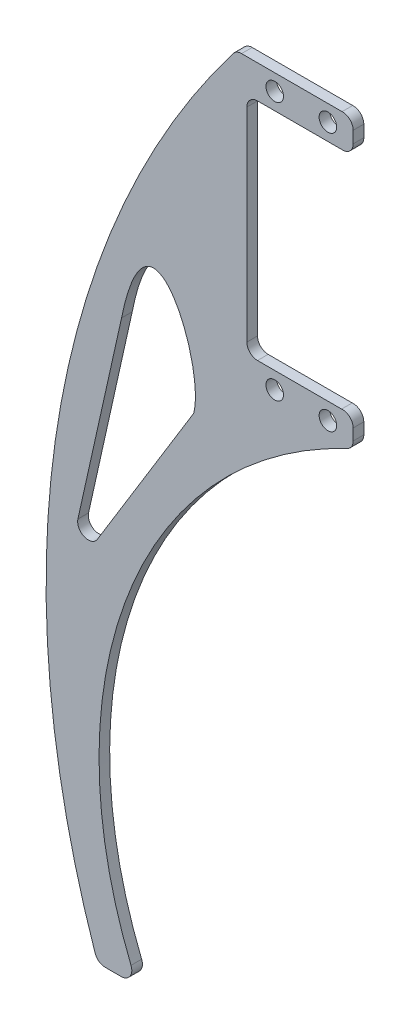
SolidWorks part; units mm, degrees
ref_plane "前视基准面" through (0, 0, 0) normal (0, 0, 1) x (1, 0, 0)
ref_plane "上视基准面" through (0, 0, 0) normal (0, 1, 0) x (1, 0, 0)
ref_plane "右视基准面" through (0, 0, 0) normal (1, 0, 0) x (0, 0, -1)
sketch "草图1" plane through (0, 0, 0) normal (0, 0, 1) x (1, 0, 0)
  line L0 (1.4233, 0) -> (4.4233, 0)
  line L1 (27.0735, 161.7067) -> (45.9834, 161.7067)
  line L3 (48.0729, 111.2078) -> (48.0729, 109.0876)
  line L4 (46.203, 155.5) -> (30.0729, 155.5)
  line L5 (-3.7143, 70.4778) -> (4.4985, 107.3478)
  line L7 (28.0729, 153.5) -> (28.0729, 115.2)
  line L8 (-0.0567, 68.9983) -> (18.0694, 98.5883)
  line L10 (48.0729, 159.7087) -> (48.0729, 157.4958)
  line L12 (30.0729, 113.2) -> (45.8963, 113.2)
  arc A0 (-0.4691, 1.3526) -> (25.4839, 160.9205) centre (161.774, 56.8591) cw
  arc A1 (6.2759, 2.7536) -> (46.9295, 107.2803) centre (81.8952, 33.512) cw
  arc A2 (48.0729, 111.2078) -> (45.8963, 113.2) centre (46.0729, 111.2078) ccw
  arc A3 (28.0729, 153.5) -> (30.0729, 155.5) centre (30.0729, 153.5) cw
  arc A4 (30.0729, 113.2) -> (28.0729, 115.2) centre (30.0729, 115.2) cw
  arc A5 (48.0729, 109.0876) -> (46.9295, 107.2803) centre (46.0729, 109.0876) cw
  arc A6 (48.0729, 159.7087) -> (45.9834, 161.7067) centre (46.0729, 159.7087) ccw
  arc A7 (46.203, 155.5) -> (48.0729, 157.4958) centre (46.0729, 157.4958) ccw
  arc A8 (27.0735, 161.7067) -> (25.4839, 160.9205) centre (27.0735, 159.7067) ccw
  arc A9 (4.4233, 0) -> (6.2759, 2.7536) centre (4.4233, 2) ccw
  arc A10 (1.4233, 0) -> (-0.4691, 1.3526) centre (1.4233, 2) cw
  arc A11 (-3.7143, 70.4778) -> (-0.0567, 68.9983) centre (-1.7622, 70.043) ccw
  spline S0 degree 3 poles (4.4985, 107.3478) (9.6506, 132.9631) (20.377, 107.57) (18.0694, 98.5883) knots 0 0 0 0 1 1 1 1
  point P9 (48.0729, 113.2)
  point P15 (28.0729, 155.5)
  point P18 (28.0729, 111.2)
  point P21 (48.0729, 155.5)
  point P32 (0, 0)
  point P47 (48.0729, 155.5)
  dimension "D5" = 2
  dimension "D6" = 2
  dimension "D7" = 2
  dimension "D8" = 2
  dimension "D2" = 20
  dimension "D3" = 161.7067
  dimension "D4" = 2
  dimension "D9" = 2
  dimension "D10" = 2
  dimension "D11" = 2
  dimension "D13" = 2
  dimension "D14" = 2
  dimension "D12" = 42.3
  dimension "D15" = 3
extrude "凸台-拉伸1" add sketch "草图1" along normal blind 2
sketch "草图2" plane through (0, 0, 2) normal (0, 0, 1) x (1, 0, 0)
  line L0 (-7.3632, 134.35) -> (80.1243, 134.35) construction
  line L1 (28.0729, 115.2) -> (28.0729, 153.5) construction
  line L3 (45.8963, 113.2) -> (30.0729, 113.2) construction
  circle A0 centre (43.3162, 158.665) radius 1.65
  circle A1 centre (33.3162, 158.665) radius 1.65
  circle A2 centre (43.3162, 110.035) radius 1.65
  circle A3 centre (33.3162, 110.035) radius 1.65
  dimension "D1" = 3.3
  dimension "D2" = 3.3
  dimension "D3" = 10
  dimension "D4" = 21.15
  dimension "D5" = 48.63
extrude "切除-拉伸1" cut sketch "草图2" against normal through all
